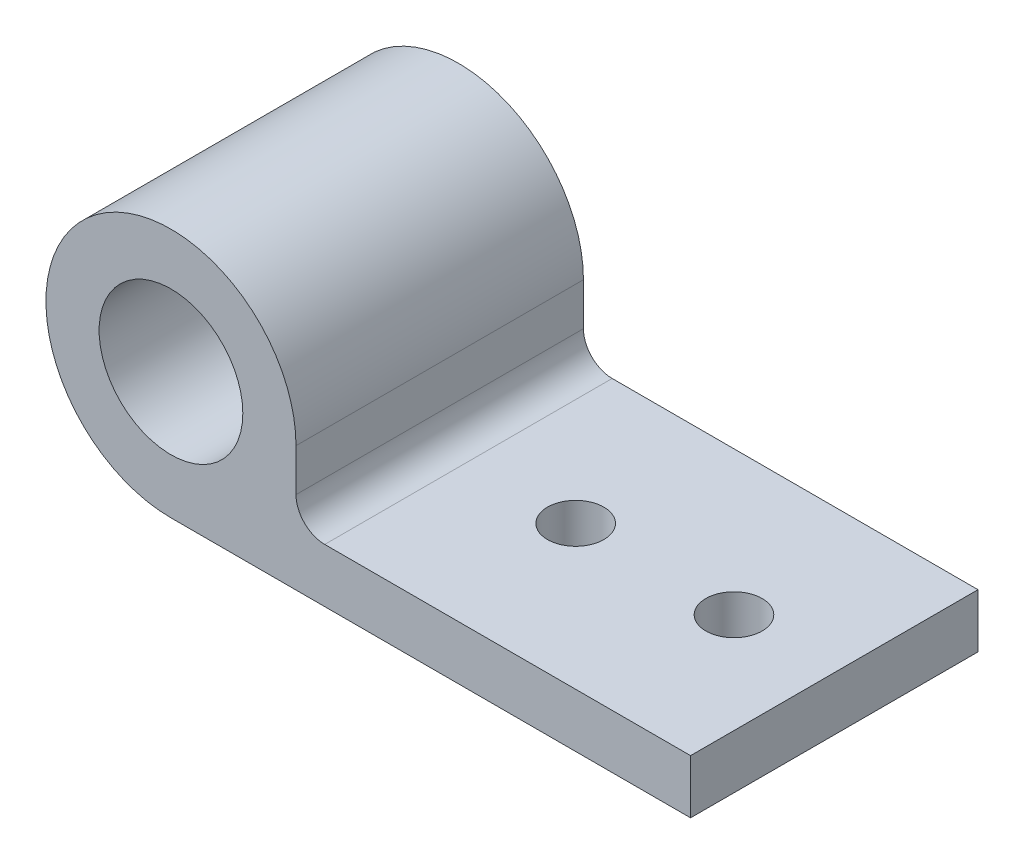
SolidWorks part; units mm, degrees
ref_plane "Front Plane" through (0, 0, 0) normal (0, 0, 1) x (1, 0, 0)
ref_plane "Top Plane" through (0, 0, 0) normal (0, 1, 0) x (1, 0, 0)
ref_plane "Right Plane" through (0, 0, 0) normal (1, 0, 0) x (0, 0, -1)
sketch "Sketch1" plane through (0, 0, 0) normal (0, 0, 1) x (1, 0, 0)
  line L0 (0, -11.049) -> (45.9163, -11.049)
  line L1 (45.9163, -11.049) -> (45.9163, -6.2865)
  line L2 (11.049, -6.2865) -> (45.9163, -6.2865)
  line L3 (11.049, 0) -> (11.049, -6.2865)
  line L4 (0, -6.223) -> (-19.8931, -6.223) construction
  line L5 (0, 0.2609) -> (0, 50000.2609) construction
  circle A0 centre (0, 0) radius 11.049
  circle A1 centre (0, 0.127) radius 6.35
  dimension "D1" = 45.9163
  dimension "D3" = 22.098
  dimension "D4" = 12.7
  dimension "D2" = 4.7625
  dimension "D5" = 4.826
extrude "Boss-Extrude1" add sketch "Sketch1" along normal blind 25.4
fillet "Fillet1" radius 2.54 1 edges at (11.049, -6.2865, 12.7)
sketch "Sketch2" plane through (0, -6.2865, 0) normal (0, 1, 0) x (1, 0, 0)
  circle A0 centre (37.0529, -12.7) radius 2.4892
  circle A1 centre (23.0632, -12.7) radius 2.4892
  dimension "D1" = 4.9784
  dimension "D2" = 4.9784
extrude "Cut-Extrude1" cut sketch "Sketch2" against normal through all
